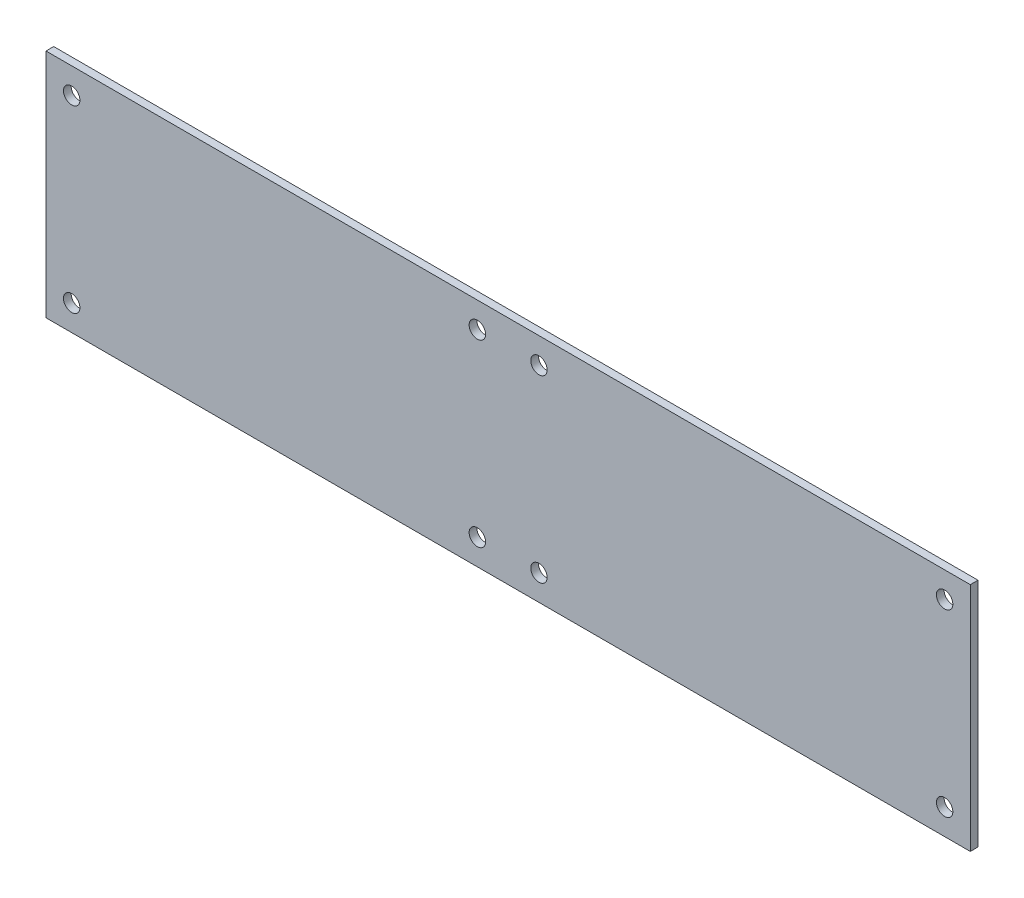
SolidWorks part; units mm, degrees
ref_plane "Front Plane" through (0, 0, 0) normal (0, 0, 1) x (1, 0, 0)
ref_plane "Top Plane" through (0, 0, 0) normal (0, 1, 0) x (1, 0, 0)
ref_plane "Right Plane" through (0, 0, 0) normal (1, 0, 0) x (0, 0, -1)
sketch "Esquisse1" plane through (0, 0, 0) normal (0, 0, 1) x (1, 0, 0)
  line L1 (-90, 22.5) -> (90, 22.5)
  line L2 (-90, 22.5) -> (-90, -22.5)
  line L3 (-90, -22.5) -> (90, -22.5)
  line L4 (90, 22.5) -> (90, -22.5)
  circle A0 centre (-85, 17.5) radius 1.6
  circle A1 centre (-85, -17.5) radius 1.6
  circle A2 centre (85, -17.5) radius 1.6
  circle A3 centre (85, 17.5) radius 1.6
  circle A4 centre (-6, 17.5) radius 1.6
  circle A5 centre (-6, -17.5) radius 1.6
  circle A6 centre (6, -17.5) radius 1.6
  circle A7 centre (6, 17.5) radius 1.6
  point P4 (-90, 0)
  point P5 (0, -22.5)
  dimension "D3" = 3.2
  dimension "D1" = 180
  dimension "D2" = 45
  dimension "D4" = 5
  dimension "D5" = 5
  dimension "D6" = 5
  dimension "D7" = 5
  dimension "D8" = 79
  dimension "D9" = 79
extrude "Main" add sketch "Esquisse1" along normal blind 1.5
